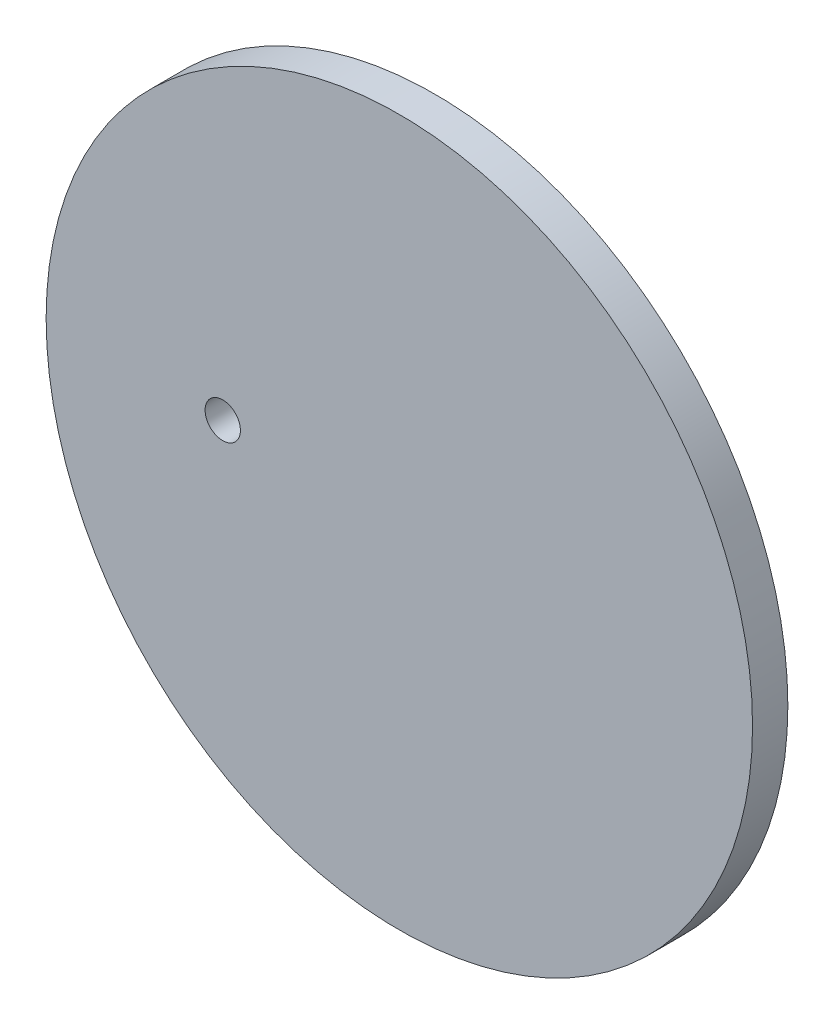
SolidWorks part; units mm, degrees
ref_plane "前视基准面" through (0, 0, 0) normal (0, 0, 1) x (1, 0, 0)
ref_plane "上视基准面" through (0, 0, 0) normal (0, 1, 0) x (1, 0, 0)
ref_plane "右视基准面" through (0, 0, 0) normal (1, 0, 0) x (0, 0, -1)
sketch "草图1" plane through (0, 0, 0) normal (0, 0, 1) x (1, 0, 0)
  circle A0 centre (0, 0) radius 40
  circle A1 centre (-20, 0) radius 2
  dimension "D2" = 4
  dimension "D3" = 80
  dimension "D1" = 20
extrude "凸台-拉伸1" add sketch "草图1" along normal mid plane 4
